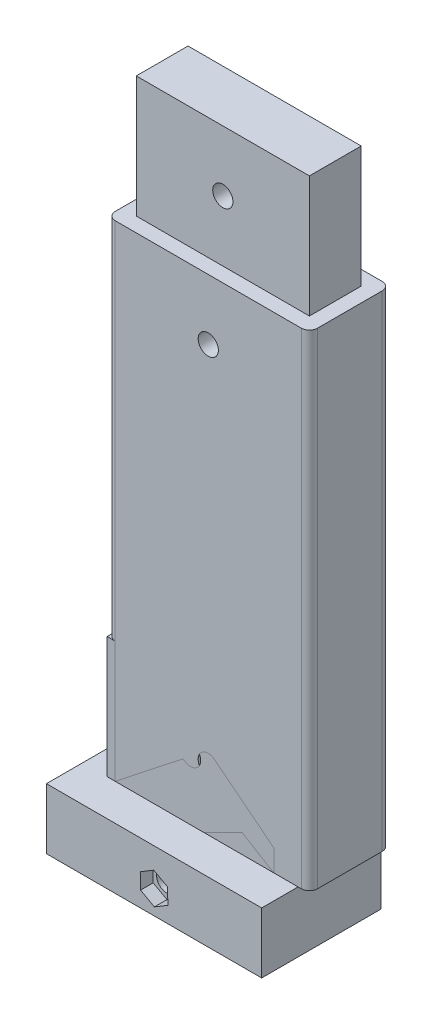
SolidWorks part; units mm, degrees
ref_plane "Front Plane" through (0, 0, 0) normal (0, 0, 1) x (1, 0, 0)
ref_plane "Top Plane" through (0, 0, 0) normal (0, 1, 0) x (1, 0, 0)
ref_plane "Right Plane" through (0, 0, 0) normal (1, 0, 0) x (0, 0, -1)
sketch "Sketch1" plane through (0, 0, 0) normal (0, 1, 0) x (1, 0, 0)
  line L1 (2, 0) -> (48, 0)
  line L2 (0, 2) -> (0, 18)
  line L3 (2, 20) -> (48, 20)
  line L4 (50, 2) -> (50, 18)
  arc A0 (2, 0) -> (0, 2) centre (2, 2) cw
  arc A1 (48, 0) -> (50, 2) centre (48, 2) ccw
  arc A2 (48, 20) -> (50, 18) centre (48, 18) cw
  arc A3 (0, 18) -> (2, 20) centre (2, 18) cw
  point P7 (0, 0)
  point P12 (50, 20)
  point P15 (0, 20)
  dimension "D3" = 2
  dimension "D1" = 50
  dimension "D2" = 20
extrude "Boss-Extrude1" add sketch "Sketch1" along normal blind 120
sketch "Sketch3" plane through (0, 0, 0) normal (0, -1, 0) x (1, 0, 0)
  line L29 (46, -16) -> (46, -4)
  line L30 (4, -16) -> (46, -16)
  line L31 (4, -4) -> (4, -16)
  line L32 (46, -4) -> (4, -4)
  line L33 (46, -16) -> (46, -4)
  line L34 (4, -16) -> (46, -16)
  line L35 (4, -4) -> (4, -16)
  line L36 (46, -4) -> (4, -4)
  dimension "D1" = 4
extrude "Cut-Extrude2" cut sketch "Sketch3" against normal blind 30 contours L35 L34 L33 L36
sketch "Sketch6" plane through (0, 0, 0) normal (0, 0, 1) x (1, 0, 0)
  line L0 (50, 120) -> (50, 0) construction
  line L1 (2, 120) -> (48, 120) construction
  line L2 (2, 0) -> (48, 0) construction
  circle A0 centre (25, 105) radius 2.5
  circle A1 centre (25, 15) radius 2.5
  dimension "D1" = 25
  dimension "D3" = 15
  dimension "D2" = 15
extrude "Cut-Extrude3" cut sketch "Sketch6" against normal blind 30
sketch "Sketch8" plane through (0, 120, 0) normal (0, 1, 0) x (1, 0, 0)
  line L20 (3.6, 16.4) -> (3.6, 3.6)
  line L21 (3.6, 3.6) -> (46.4, 3.6)
  line L22 (46.4, 3.6) -> (46.4, 16.4)
  line L23 (46.4, 16.4) -> (3.6, 16.4)
  line L24 (3.6, 16.4) -> (3.6, 3.6)
  line L25 (3.6, 3.6) -> (46.4, 3.6)
  line L26 (46.4, 3.6) -> (46.4, 16.4)
  line L27 (46.4, 16.4) -> (3.6, 16.4)
  dimension "D1" = 3.6
extrude "Boss-Extrude2" add sketch "Sketch8" along normal blind 30
sketch "Sketch9" plane through (0, 0, -3.6) normal (0, 0, 1) x (1, 0, 0)
  line L0 (46.4, 150) -> (46.4, 120) construction
  line L1 (3.6, 150) -> (46.4, 150) construction
  circle A0 centre (25, 135) radius 2.5
  dimension "D1" = 21.4
  dimension "D2" = 15
extrude "Cut-Extrude4" cut sketch "Sketch9" against normal blind 30
sketch "Sketch11" plane through (0, 0, 0) normal (0, 1, 0) x (1, 0, 0)
  line L1 (0, 0) -> (41.2, 0)
  line L2 (0, 0) -> (0, 11.5)
  line L3 (0, 11.5) -> (41.2, 11.5)
  line L4 (41.2, 0) -> (41.2, 11.5)
  dimension "D1" = 41.2
  dimension "D2" = 11.5
extrude "Boss-Extrude3" add sketch "Sketch11" along normal blind 30 separate body
hole_wizard "Ø5.0 (5) Diameter Hole1" positions "Sketch12" profile "Sketch13" hole size "Ø5.0" standard "ANSI Metric" end condition through all
sketch "Sketch12" plane through (0, 0, 0) normal (0, 0, 1) x (1, 0, 0)
  line L0 (0, 30) -> (41.2, 30) construction
  line L1 (41.2, 30) -> (41.2, 0) construction
  point P0 (20.6, 15)
  dimension "D1" = 15
  dimension "D2" = 20.6
sketch "Sketch13" plane through (20.6, 15, 0) normal (1, 0, 0) x (0, -1, 0)
  line L0 (0, 0) -> (0, 20)
  line L1 (0, 20) -> (2.5, 20)
  line L2 (2.5, 20) -> (2.5, 0.021)
  line L3 (2.5, 0.021) -> (2.525, 0)
  line L5 (2.525, 0) -> (0, 0)
  line L6 (-2.5, 0.021) -> (-2.525, 0) construction
  line L11 (0, -6.35) -> (0, 107.95) construction
  dimension "Thru Hole Dia." = 5
  dimension "Thru Hole Depth" = 20
  dimension "Near C'Sink Dia." = 5.05
  dimension "Near C'Sink Angle" = 100
sketch "Sketch15" plane through (0, 0, 0) normal (0, 0, 1) x (1, 0, 0)
  line L0 (0, 0) -> (0, -15.1097)
  line L1 (41.2, 0) -> (41.2, -15.1097)
  line L2 (0, 0) -> (41.2, 0)
  arc A0 (0, -15.1097) -> (41.2, -15.1097) centre (20.6, -23.3449) cw
extrude "Boss-Extrude4" add sketch "Sketch15" against normal blind 14.5 and the other way blind 3 contours L0 A0 L1 L2
sketch "Sketch16" plane through (0, 0, 0) normal (0, 1, 0) x (1, 0, 0)
  line L37 (0, 14.5) -> (41.2, 14.5)
  line L38 (0, 14.5) -> (0, -3)
  line L39 (0, -3) -> (41.2, -3)
  line L40 (41.2, 14.5) -> (41.2, -3)
  line L44 (-6, 20.5) -> (-6, 11.5)
  line L45 (-6, 11.5) -> (-6, 0)
  line L46 (-6, 0) -> (-6, -9)
  line L47 (-6, -9) -> (47.2, -9)
  line L48 (47.2, -9) -> (47.2, 0)
  line L49 (47.2, 0) -> (47.2, 11.5)
  line L50 (47.2, 11.5) -> (47.2, 20.5)
  line L51 (47.2, 20.5) -> (-6, 20.5)
  line L52 (-6, 20.5) -> (-6, 11.5)
  line L53 (-6, 11.5) -> (-6, 0)
  line L54 (-6, 0) -> (-6, -9)
  line L55 (-6, -9) -> (47.2, -9)
  line L56 (47.2, -9) -> (47.2, 0)
  line L57 (47.2, 0) -> (47.2, 11.5)
  line L58 (47.2, 11.5) -> (47.2, 20.5)
  line L59 (47.2, 20.5) -> (-6, 20.5)
  dimension "D1" = 6
extrude "Boss-Extrude5" add sketch "Sketch16" against normal blind 15
hole_wizard "Ø5.0 (5) Diameter Hole2" positions "Sketch17" profile "Sketch18" hole size "Ø5.0" standard "ANSI Metric" end condition through all
sketch "Sketch17" plane through (0, 0, -20.5) normal (0, 0, -1) x (-1, 0, 0)
  line L0 (6, -15) -> (6, 0) construction
  point P0 (-20.6, -9.147)
  dimension "D1" = 26.6
sketch "Sketch18" plane through (20.6, -9.147, -20.5) normal (1, 0, 0) x (0, 1, 0)
  line L0 (0, 0) -> (0, 29.5)
  line L1 (0, 29.5) -> (2.5, 29.5)
  line L2 (2.5, 29.5) -> (2.5, 0.021)
  line L3 (2.5, 0.021) -> (2.525, 0)
  line L5 (2.525, 0) -> (0, 0)
  line L6 (-2.5, 0.021) -> (-2.525, 0) construction
  line L11 (0, -6.35) -> (0, 107.95) construction
  dimension "Thru Hole Dia." = 5
  dimension "Thru Hole Depth" = 29.5
  dimension "Near C'Sink Dia." = 5.05
  dimension "Near C'Sink Angle" = 100
sketch "Sketch22" plane through (0, 0, 9) normal (0, 0, 1) x (1, 0, 0)
  line L1 (24.0138, -11.0268) -> (23.9348, -7.1305)
  line L2 (23.9348, -7.1305) -> (20.521, -5.2507)
  line L3 (20.521, -5.2507) -> (17.1862, -7.2673)
  line L4 (17.1862, -7.2673) -> (17.2652, -11.1636)
  line L5 (17.2652, -11.1636) -> (20.679, -13.0433)
  line L6 (20.679, -13.0433) -> (24.0138, -11.0268)
  circle A0 centre (20.6, -9.147) radius 3.375 construction
  dimension "D1" = 6.75
extrude "Cut-Extrude5" cut sketch "Sketch22" against normal blind 3.12
